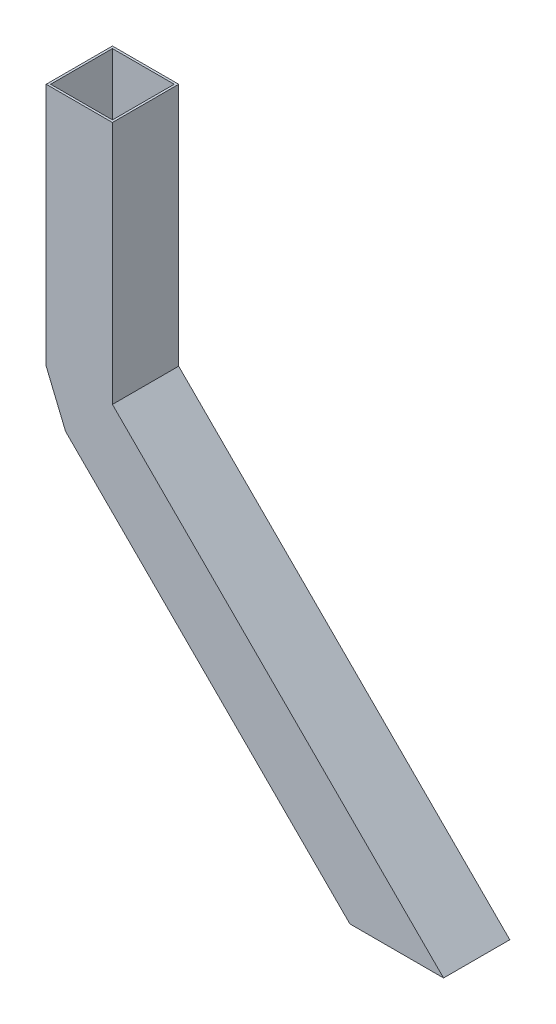
SolidWorks part; units mm, degrees
ref_plane "Alzado" through (0, 0, 0) normal (0, 0, 1) x (1, 0, 0)
ref_plane "Planta" through (0, 0, 0) normal (0, 1, 0) x (1, 0, 0)
ref_plane "Vista lateral" through (0, 0, 0) normal (1, 0, 0) x (0, 0, -1)
sketch "Croquis1" plane through (0, 0, 0) normal (0, 1, 0) x (1, 0, 0)
  line L0 (-28, -28) -> (-28, 28)
  line L1 (-30, -30) -> (30, -30)
  line L2 (-30, -30) -> (-30, 30)
  line L3 (-30, 30) -> (30, 30)
  line L4 (30, -30) -> (30, 30)
  line L5 (-30, -30) -> (30, 30) construction
  line L6 (-30, 30) -> (30, -30) construction
  line L7 (-28, 28) -> (28, 28)
  line L8 (28, -28) -> (28, 28)
  line L9 (-28, -28) -> (28, -28)
  point P0 (0, 0)
  dimension "D1" = 60
  dimension "D2" = 60
  dimension "D3" = 2
extrude "Saliente-Extruir1" add sketch "Croquis1" along normal blind 221.22
sketch "Croquis2" plane through (0, 0, 0) normal (0, 0, 1) x (1, 0, 0)
  line L0 (0, 0) -> (187.7661, -187.7661) construction
  line L1 (0, 0) -> (0, 215.4018) construction
  point P5 (0, 215.4018)
  dimension "D1" = 135
ref_plane "Plano1" through (15, -15, 0) normal (0.7071, -0.7071, 0) x (0, 0, -1)
sketch "Croquis3" plane through (15, -15, 0) normal (0.7071, -0.7071, 0) x (0, 0, -1)
  line L6 (-30, -38.7868) -> (30, -38.7868)
  line L10 (-30, -38.7868) -> (-30, 21.2132)
  line L11 (-30, 21.2132) -> (30, 21.2132)
  line L12 (30, -38.7868) -> (30, 21.2132)
  line L13 (-30, -38.7868) -> (30, 21.2132) construction
  line L14 (-30, 21.2132) -> (30, -38.7868) construction
  line L18 (-30, 21.2132) -> (30, 21.2132) construction
  line L19 (30, 21.2132) -> (30, -21.2132) construction
  line L20 (-28, 19.2132) -> (28, 19.2132)
  line L21 (28, -36.7868) -> (28, 19.2132)
  line L22 (-28, -36.7868) -> (28, -36.7868)
  line L23 (-28, -36.7868) -> (-28, 19.2132)
  point P0 (0, -8.7868)
  dimension "D1" = 60
  dimension "D2" = 60
  dimension "D3" = 2
extrude "Saliente-Extruir2" add sketch "Croquis3" along normal blind 424.26
sketch "Croquis10" plane through (0, 0, 30) normal (0, 0, 1) x (1, 0, 0)
  line L4 (287.5707, -342.4235) -> (329.9971, -299.9971)
  line L5 (329.9971, -299.9971) -> (245.1443, -299.9971)
  line L6 (287.5707, -342.4235) -> (-12.4264, -42.4264) construction
  line L7 (245.1443, -299.9971) -> (287.5707, -342.4235)
extrude "Cortar-Extruir1" cut sketch "Croquis10" against normal through all
sketch "Croquis13" plane through (0, 0, 30) normal (0, 0, 1) x (1, 0, 0)
  line L4 (-12.4264, -42.4264) -> (-30, 0)
sketch "Croquis14" plane through (15, -15, 0) normal (-0.7071, 0.7071, 0) x (0, 0, 1)
  line L0 (30, -38.7868) -> (-30, -38.7868)
  line L1 (-30, -38.7868) -> (-30, 21.2132)
  line L2 (-30, 21.2132) -> (30, 21.2132)
  line L3 (30, 21.2132) -> (30, -38.7868)
  line L4 (28, -36.7868) -> (-28, -36.7868)
  line L5 (-28, -36.7868) -> (-28, 19.2132)
  line L6 (-28, 19.2132) -> (28, 19.2132)
  line L7 (28, 19.2132) -> (28, -36.7868)
sweep "Barrer2" add profiles "Croquis14" path "Croquis13"
sketch "Croquis11" plane through (0, 0, 0) normal (0, 1, 0) x (1, 0, 0)
  circle A0 centre (0, 0) radius 8.2422 construction
sketch "Croquis12" plane through (0, 0, 0) normal (0, 0, 1) x (1, 0, 0)
  line L0 (0, 0) -> (-257.5495, -257.5495) construction
  dimension "D1" = 364.23
